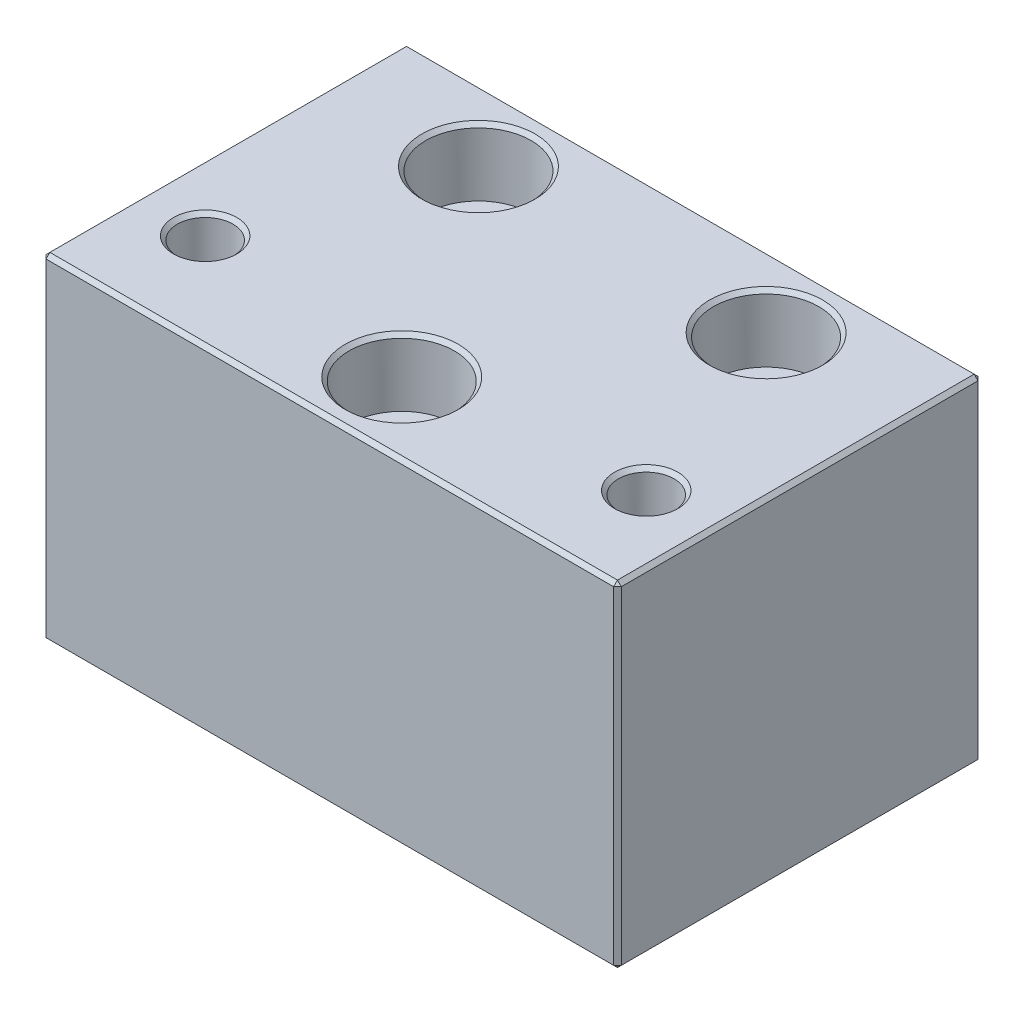
SolidWorks part; units mm, degrees
ref_plane "Front Plane" through (0, 0, 0) normal (0, 0, 1) x (1, 0, 0)
ref_plane "Top Plane" through (0, 0, 0) normal (0, 1, 0) x (1, 0, 0)
ref_plane "Right Plane" through (0, 0, 0) normal (1, 0, 0) x (0, 0, -1)
sketch "Sketch1" plane through (0, 0, 0) normal (0, 1, 0) x (1, 0, 0)
  line L1 (30, 19) -> (-30, 19)
  line L2 (30, 19) -> (30, -19)
  line L3 (30, -19) -> (-30, -19)
  line L4 (-30, 19) -> (-30, -19)
  line L5 (30, 19) -> (-30, -19) construction
  line L6 (30, -19) -> (-30, 19) construction
  point P0 (0, 0)
  dimension "D1" = 38
  dimension "D2" = 60
extrude "Boss-Extrude1" add sketch "Sketch1" along normal blind 35
sketch "Sketch2" plane through (0, 35, 0) normal (0, 1, 0) x (1, 0, 0)
  line L0 (-30, -19) -> (30, -19) construction
  line L1 (-23, -9) -> (23, -9) construction
  line L2 (0, 0) -> (0, -9) construction
  line L3 (0, -11.5) -> (0, -9) construction
  line L4 (30, 19) -> (-30, 19) construction
  circle A0 centre (-23, -9) radius 2.9
  circle A1 centre (23, -9) radius 2.9
  circle A2 centre (-15, 11.5) radius 3.05
  circle A3 centre (0, -11.5) radius 3.05
  circle A4 centre (15, 11.5) radius 3.05
  dimension "D1" = 5.8
  dimension "D4" = 6.1
  dimension "D2" = 10
  dimension "D3" = 46
  dimension "D5" = 7.5
  dimension "D6" = 7.5
  dimension "D7" = 15
extrude "Cut-Extrude1" cut sketch "Sketch2" against normal through all
sketch "Sketch3" plane through (0, 35, 0) normal (0, 1, 0) x (1, 0, 0)
  circle A0 centre (-15, 11.5) radius 5.5
  circle A1 centre (15, 11.5) radius 5.5
  circle A2 centre (0, -11.5) radius 5.5
  dimension "D1" = 11
extrude "Cut-Extrude2" cut sketch "Sketch3" against normal blind 7
chamfer "Chamfer1" distance 0.4 angle 45 17 edges at (0, 35, 17) (15, 35, -6) (-15, 35, -6) (23, 35, 11.9) (-23, 35, 11.9) (0, 35, 19) (0, 0, 19) (-30, 35, 0) (-30, 17.5, 19) (-30, 0, 0) (0, 35, -19) (-30, 17.5, -19) (0, 0, -19) (30, 17.5, 19) (30, 35, 0) (30, 17.5, -19) (30, 0, 0)
